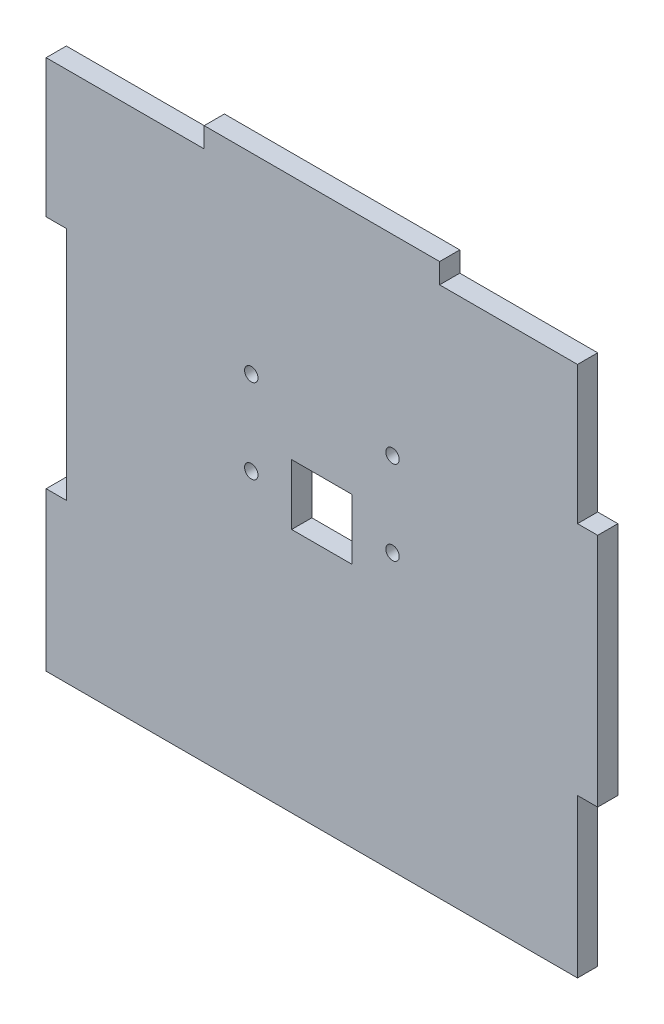
SolidWorks part; units mm, degrees
ref_plane "Front Plane" through (0, 0, 0) normal (0, 0, 1) x (1, 0, 0)
ref_plane "Top Plane" through (0, 0, 0) normal (0, 1, 0) x (1, 0, 0)
ref_plane "Right Plane" through (0, 0, 0) normal (1, 0, 0) x (0, 0, -1)
sketch "Sketch1" plane through (0, 0, 0) normal (0, 0, 1) x (1, 0, 0)
  line L0 (0, 38) -> (0, -39.5) construction
  line L5 (-38, 39.5) -> (-17.5, 39.5)
  line L6 (-38, 16) -> (-38, -16)
  line L24 (38, 39.5) -> (38, 19)
  line L26 (-41, -39.5) -> (38, -39.5)
  line L27 (-38, 0) -> (38, 0) construction
  line L28 (-17.5, 39.5) -> (-17.5, 42.5)
  line L29 (-17.5, 42.5) -> (17.5, 42.5)
  line L30 (17.5, 42.5) -> (17.5, 39.5)
  line L33 (-41, 19) -> (-41, 39.5)
  line L34 (-41, 39.5) -> (-38, 39.5)
  line L35 (-41, -19) -> (-41, -39.5)
  line L36 (38, -19) -> (38, -39.5)
  line L43 (41, 16) -> (41, -16)
  line L44 (-38, 16) -> (-38, 19)
  line L46 (17.5, 39.5) -> (38, 39.5)
  line L48 (-38, 19) -> (-41, 19)
  line L50 (-41, -19) -> (-41, -16)
  line L51 (-41, -16) -> (-38, -16)
  line L52 (38, -19) -> (38, -16)
  line L53 (38, -16) -> (41, -16)
  line L54 (41, 16) -> (41, 19)
  line L55 (41, 19) -> (38, 19)
  point P0 (0, 0)
  dimension "D1" = 79
  dimension "D2" = 76
  dimension "D3" = 3
  dimension "D4" = 35
  dimension "D5" = 3
  dimension "D6" = 76
  dimension "D7" = 35
  dimension "D8" = 3
  dimension "D9" = 3
  dimension "D10" = 3
  dimension "D11" = 3
  dimension "D12" = 35
  dimension "D13" = 0
  dimension "D14" = 20.5
extrude "Boss-Extrude1" add sketch "Sketch1" along normal blind 3
sketch "Sketch2" plane through (0, 0, 3) normal (0, 0, 1) x (1, 0, 0)
  line L0 (-41, -39.5) -> (38, -39.5) construction
  line L5 (-4, 5.5) -> (4, 5.5) construction
  line L6 (-4, 5.5) -> (-4, -2.5) construction
  line L7 (-4, -2.5) -> (4, -2.5) construction
  line L8 (4, 5.5) -> (4, -2.5) construction
  line L9 (-4, 5.5) -> (4, -2.5) construction
  line L10 (-4, -2.5) -> (4, 5.5) construction
  line L11 (0, 16) -> (0, -8) construction
  line L12 (-12.5, -8) -> (12.5, -8) construction
  line L13 (-12.5, -8) -> (-12.5, 16) construction
  line L14 (-12.5, 16) -> (12.5, 16) construction
  line L15 (12.5, -8) -> (12.5, 16) construction
  line L16 (-12.5, -8) -> (12.5, 16) construction
  line L17 (-12.5, 16) -> (12.5, -8) construction
  line L18 (-4.5, -3) -> (4.5, -3)
  line L19 (-4.5, -3) -> (-4.5, 6)
  line L20 (-4.5, 6) -> (4.5, 6)
  line L21 (4.5, -3) -> (4.5, 6)
  line L22 (-4.5, -3) -> (4.5, 6) construction
  line L23 (-4.5, 6) -> (4.5, -3) construction
  circle A4 centre (-10.5, 14) radius 1
  circle A5 centre (-10.5, 1.5) radius 1
  circle A6 centre (10.5, 1.5) radius 1
  circle A7 centre (10.5, 14) radius 1
  point P0 (0, 0)
  point P1 (0, 1.5)
  point P9 (0, 4)
  point P18 (0, 1.5)
  dimension "D9" = 2
  dimension "D12" = 2
  dimension "D1" = 8
  dimension "D2" = 8
  dimension "D3" = 0
  dimension "D4" = 41
  dimension "D5" = 25
  dimension "D6" = 24
  dimension "D7" = 0
  dimension "D8" = 5.5
  dimension "D10" = 2
  dimension "D11" = 2
  dimension "D13" = 2
  dimension "D14" = 12.5
  dimension "D15" = 9
  dimension "D16" = 9
extrude "Cut-Extrude1" cut sketch "Sketch2" against normal blind 3
